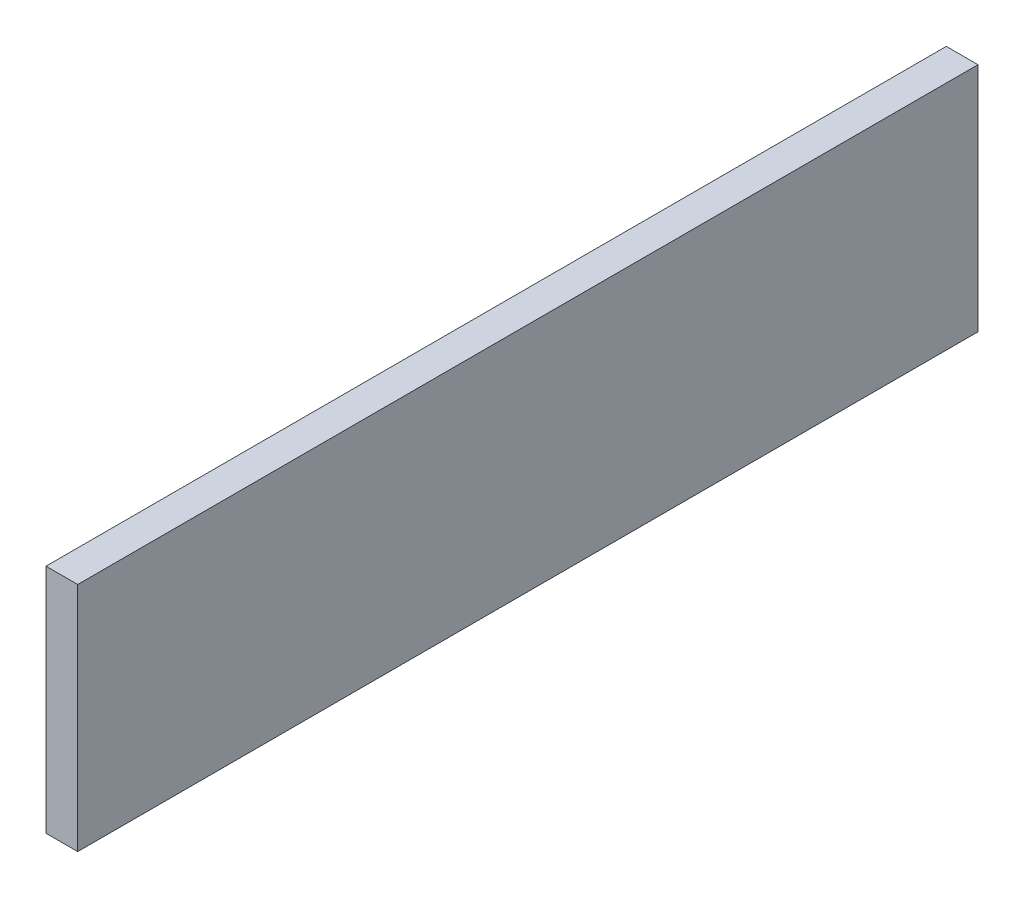
SolidWorks part; units mm, degrees
material "Maple"
ref_plane "Front Plane" through (0, 0, 0) normal (0, 0, 1) x (1, 0, 0)
ref_plane "Top Plane" through (0, 0, 0) normal (0, 1, 0) x (1, 0, 0)
ref_plane "Right Plane" through (0, 0, 0) normal (1, 0, 0) x (0, 0, -1)
sketch "Sketch1" plane through (0, 0, 0) normal (0, 0, 1) x (1, 0, 0)
  line L1 (-1.5875, 11.585) -> (1.5875, 11.585)
  line L2 (-1.5875, 11.585) -> (-1.5875, -11.585)
  line L3 (-1.5875, -11.585) -> (1.5875, -11.585)
  line L4 (1.5875, 11.585) -> (1.5875, -11.585)
  line L5 (-1.5875, 11.585) -> (1.5875, -11.585) construction
  line L6 (-1.5875, -11.585) -> (1.5875, 11.585) construction
  point P0 (0, 0)
  dimension "D1" = 3.175
  dimension "D2" = 23.17
extrude "Boss-Extrude1" add sketch "Sketch1" along normal blind 90.17
equation "\"kerf\"= 0.17 / 2"
